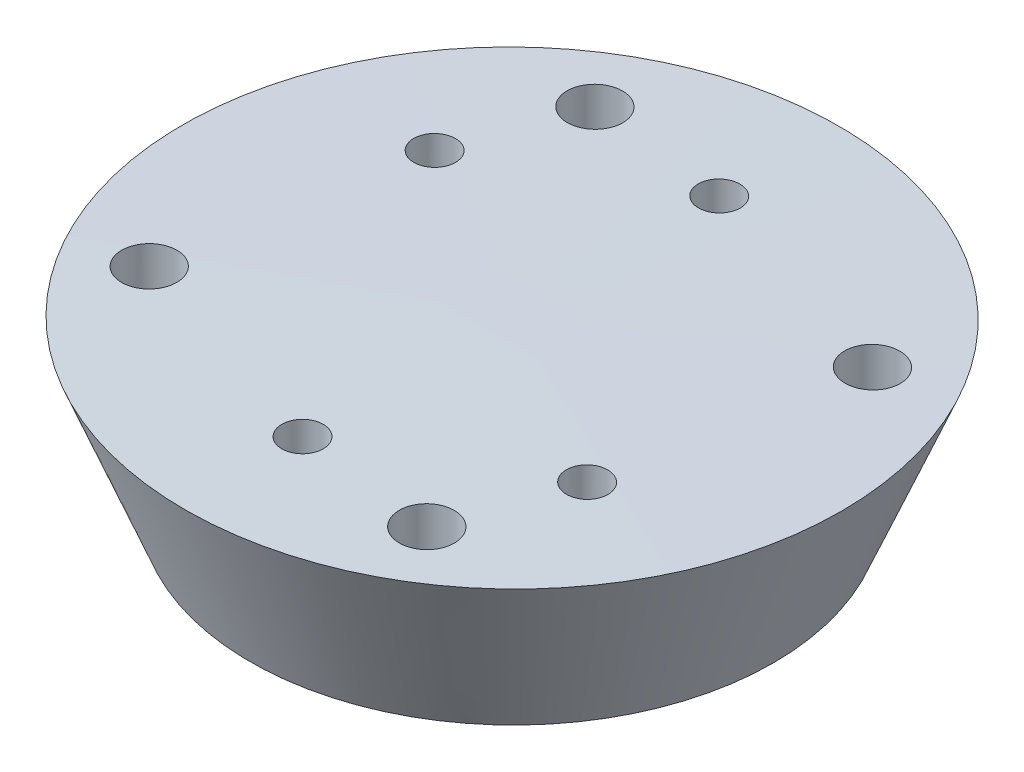
SolidWorks part; units mm, degrees
ref_plane "Piano frontale" through (0, 0, 0) normal (0, 0, 1) x (1, 0, 0)
ref_plane "Piano superiore" through (0, 0, 0) normal (0, 1, 0) x (1, 0, 0)
ref_plane "Piano destro" through (0, 0, 0) normal (1, 0, 0) x (0, 0, -1)
sketch "Schizzo1" plane through (0, 0, 0) normal (0, 0, 1) x (1, 0, 0)
  line L0 (0, -101.5) -> (0.1474, -81.5)
  line L1 (31.5, -101.5) -> (-31.5, -101.5) construction
  line L2 (-39.1051, -81.5) -> (39.4, -81.5) construction
  line L3 (0.1474, -81.5) -> (-39.3999, -81.5)
  line L4 (-39.3999, -81.5) -> (-31.5, -101.5)
  line L5 (-31.5, -101.5) -> (0, -101.5)
revolve "Rivoluzione1" add sketch "Schizzo1" angle 360 about L0
sketch "Schizzo2" plane through (0, -101.5, 0) normal (0, 1, 0) x (1, 0, 0)
  circle A1 centre (21.6506, -12.5) radius 2.5
  circle A2 centre (0, -25) radius 2.5
  circle A4 centre (-21.6506, 12.5) radius 2.5
  circle A5 centre (0, 25) radius 2.5
  point P15 (0, 0)
extrude "Taglio-Estrusione1" cut sketch "Schizzo2" along normal blind 21 and the other way blind 10
sketch "Schizzo3" plane through (0, -81.5, 0) normal (0, -1, 0) x (1, 0, 0)
  arc A1 (17.4043, 23.5018) -> (15.8991, 29.9761) centre (16.6517, 26.7389) ccw construction
  arc A2 (15.8991, 29.9761) -> (17.4043, 23.5018) centre (16.6517, 26.7389) ccw construction
  arc A5 (17.4043, 23.5018) -> (15.8991, 29.9761) centre (16.6517, 26.7389) ccw
  arc A6 (15.8991, 29.9761) -> (17.4043, 23.5018) centre (16.6517, 26.7389) ccw
  arc A8 (29.9761, -15.8991) -> (23.5018, -17.4043) centre (26.7389, -16.6517) ccw
  arc A9 (23.5018, -17.4043) -> (29.9761, -15.8991) centre (26.7389, -16.6517) ccw
  arc A10 (-15.8991, -29.9761) -> (-17.4043, -23.5018) centre (-16.6517, -26.7389) ccw
  arc A11 (-17.4043, -23.5018) -> (-15.8991, -29.9761) centre (-16.6517, -26.7389) ccw
  arc A12 (-29.9761, 15.8991) -> (-23.5018, 17.4043) centre (-26.7389, 16.6517) ccw
  arc A13 (-23.5018, 17.4043) -> (-29.9761, 15.8991) centre (-26.7389, 16.6517) ccw
  point P19 (0, 0)
  dimension "D1" = 4
extrude "Taglio-Estrusione2" cut sketch "Schizzo3" along normal blind 11
